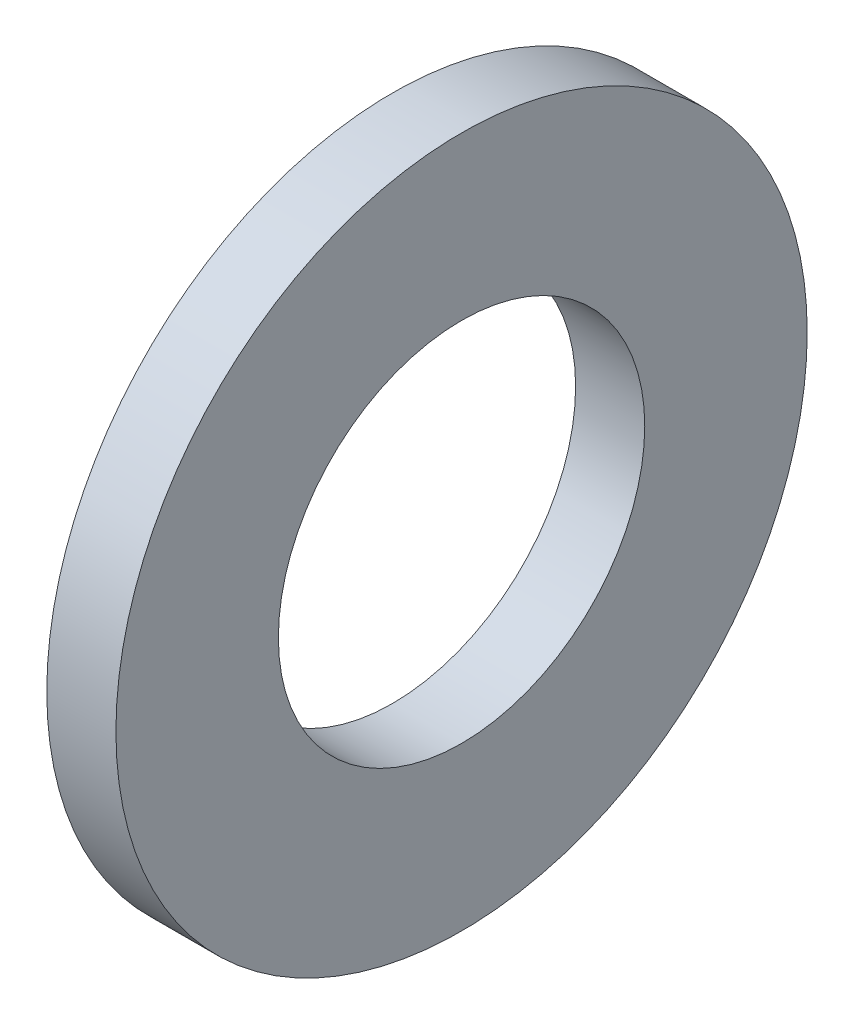
SolidWorks part; units mm, degrees
ref_plane "Plane1" through (0, 0, 0) normal (0, 0, 1) x (1, 0, 0)
ref_plane "Plane2" through (0, 0, 0) normal (0, 1, 0) x (1, 0, 0)
ref_plane "Plane3" through (0, 0, 0) normal (1, 0, 0) x (0, 0, -1)
sketch "Sketch1" plane through (0, 0, 0) normal (0, 0, 1) x (1, 0, 0)
  line L0 (-34.925, 0) -> (9.525, 0) construction
  line L1 (0, 2.65) -> (0, 5)
  line L2 (0, 5) -> (-1, 5)
  line L3 (-1, 5) -> (-1, 2.65)
  line L4 (-1, 2.65) -> (0, 2.65)
revolve "Base-Revolve" add sketch "Sketch1" angle 360 about L0
chamfer "Chamfer1" [suppressed] distance 0.375 angle 37
equation "\"D1@Chamfer1\" = \"Thickness@Sketch1\"*0.375"
